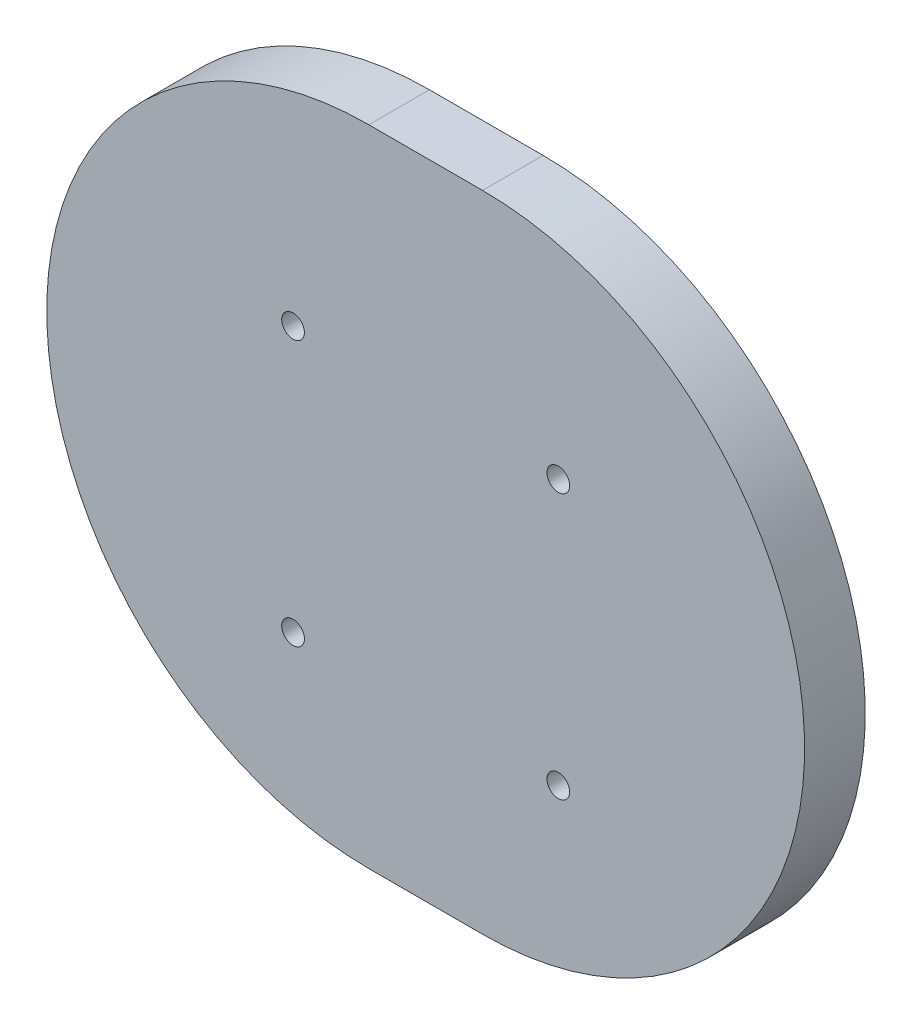
SolidWorks part; units mm, degrees
ref_plane "Front Plane" through (0, 0, 0) normal (0, 0, 1) x (1, 0, 0)
ref_plane "Top Plane" through (0, 0, 0) normal (0, 1, 0) x (1, 0, 0)
ref_plane "Right Plane" through (0, 0, 0) normal (1, 0, 0) x (0, 0, -1)
sketch "Sketch1" plane through (0, 0, 0) normal (0, 0, 1) x (1, 0, 0)
  line L0 (-1.5, 0) -> (1.5, 0) construction
  line L1 (-1.5, 8.5) -> (1.5, 8.5)
  line L2 (-1.5, -8.5) -> (1.5, -8.5)
  line L4 (3.5, -4.1) -> (-3.5, -4.1) construction
  line L5 (3.5, -4.1) -> (3.5, 2.9) construction
  line L6 (3.5, 2.9) -> (-3.5, 2.9) construction
  line L7 (-3.5, -4.1) -> (-3.5, 2.9) construction
  arc A0 (-1.5, 8.5) -> (-1.5, -8.5) centre (-1.5, 0) ccw
  arc A1 (1.5, -8.5) -> (1.5, 8.5) centre (1.5, 0) ccw
  circle A2 centre (3.5, 2.9) radius 0.3
  circle A3 centre (-3.5, 2.9) radius 0.3
  circle A4 centre (-3.5, -4.1) radius 0.3
  circle A5 centre (3.5, -4.1) radius 0.3
  point P3 (0, 0)
  point P12 (3.5, -0.6)
  point P13 (0, 2.9)
  point P14 (0, 8.5)
  dimension "D1" = 8.5
  dimension "D6" = 0.6
  dimension "D7" = 0.6
  dimension "D8" = 0.6
  dimension "D9" = 0.6
  dimension "D2" = 3
  dimension "D3" = 9.1
  dimension "D4" = 7
  dimension "D5" = 7
extrude "Boss-Extrude1" add sketch "Sketch1" along normal blind 1.6
